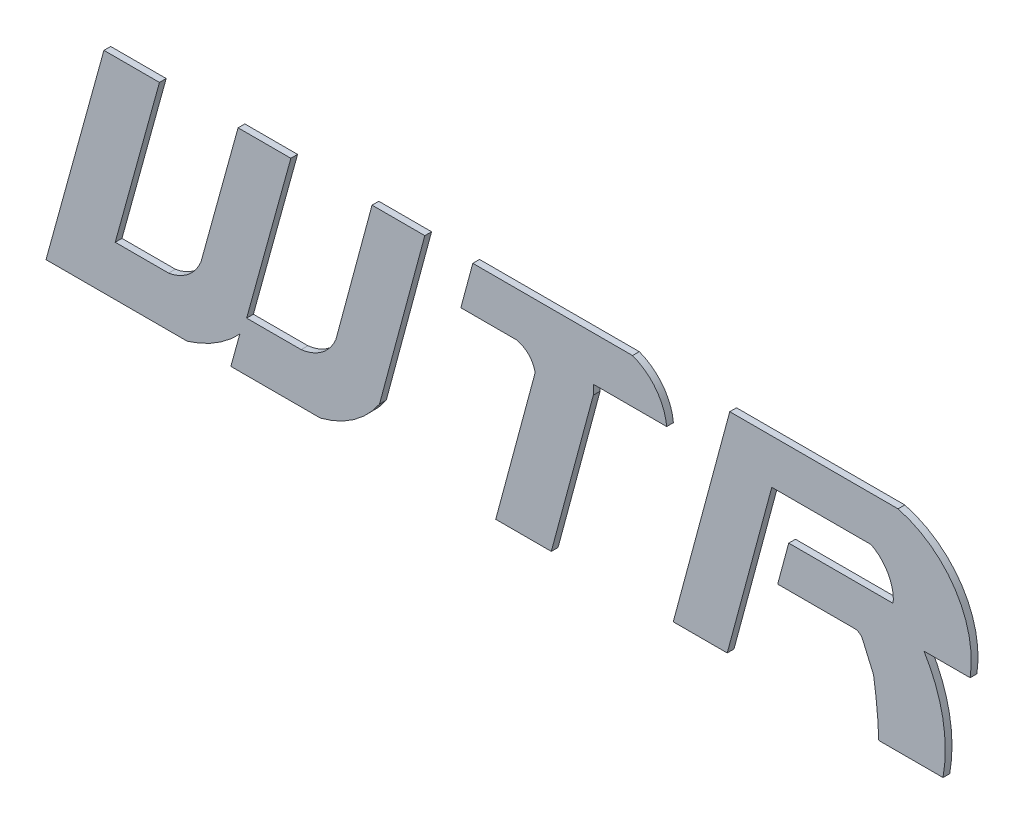
SolidWorks part; units mm, degrees
ref_plane "Front" through (0, 0, 0) normal (0, 0, 1) x (1, 0, 0)
ref_plane "Top" through (0, 0, 0) normal (0, 1, 0) x (1, 0, 0)
ref_plane "Right" through (0, 0, 0) normal (1, 0, 0) x (0, 0, -1)
sketch "草图2" plane through (0, 0, 0) normal (0, 0, 1) x (1, 0, 0)
  line L0 (341.3333, 1024) -> (1706.6667, 1024) construction
  line L1 (389.3044, 1163.2358) -> (303.4742, 851.6607)
  line L2 (303.4742, 851.6607) -> (512.7586, 851.6607)
  line L3 (577.4252, 851.6607) -> (710.2855, 851.6607)
  line L4 (389.3044, 1163.2358) -> (471.6072, 1163.2358)
  line L5 (471.6072, 1163.2358) -> (406.058, 925.2832)
  line L6 (406.058, 925.2832) -> (485.1876, 925.2832)
  line L7 (588.1245, 1163.2358) -> (533.2003, 963.8531)
  line L8 (588.1245, 1163.2358) -> (666.3345, 1163.2358)
  line L9 (666.3345, 1163.2358) -> (600.7853, 925.2832)
  line L10 (600.7853, 925.2832) -> (681.6483, 925.2832)
  line L11 (786.6575, 1163.2358) -> (733.0591, 963.8531)
  line L12 (786.6575, 1163.2358) -> (864.8674, 1163.2358)
  line L13 (864.8674, 1163.2358) -> (797.7177, 913.4432)
  line L14 (918.2572, 1097.3573) -> (935.9667, 1163.2358)
  line L15 (935.9667, 1163.2358) -> (1172.7019, 1163.2358)
  line L16 (918.2572, 1097.3573) -> (1000.5553, 1097.3573)
  line L17 (1114.5647, 1097.3573) -> (1223.2888, 1097.3573)
  line L18 (969.9365, 851.6607) -> (1028.3503, 1068.9564)
  line L19 (969.9365, 851.6607) -> (1052.2954, 851.6607)
  line L20 (1052.2954, 851.6607) -> (1114.5647, 1083.2984)
  line L21 (1114.5647, 1097.3573) -> (1114.5647, 1083.2984)
  line L22 (1316.7648, 1163.2358) -> (1233.0067, 851.6607)
  line L23 (1233.0067, 851.6607) -> (1313, 851.6607)
  line L24 (1313, 851.6607) -> (1379.0486, 1097.3573)
  line L25 (1379.0486, 1097.3573) -> (1526.2836, 1097.3573)
  line L26 (1316.7648, 1163.2358) -> (1566.1682, 1163.2358)
  line L27 (1604.5506, 999.8486) -> (1673, 999.8486)
  line L28 (1558.9709, 1038.2308) -> (1404.1293, 1038.2308)
  line L29 (1404.1293, 1038.2308) -> (1387.7741, 977.3907)
  line L30 (1387.7741, 977.3907) -> (1499.9591, 977.3907)
  line L31 (1513.7437, 969.2578) -> (1529.8482, 932.0508)
  line L32 (1537.5971, 851.6607) -> (1632.7974, 851.6607)
  line L33 (577.4252, 851.6607) -> (590.6328, 899.6064)
  arc A0 (485.1876, 925.2832) -> (533.2003, 963.8531) centre (475.2441, 986.8296) ccw
  arc A1 (681.6483, 925.2832) -> (733.0591, 963.8531) centre (674.2809, 988.6516) ccw
  arc A2 (1000.5553, 1097.3573) -> (1028.3503, 1068.9564) centre (993.9959, 1063.1364) cw
  arc A3 (1172.7019, 1163.2358) -> (1223.2888, 1097.3573) centre (1145.0074, 1089.608) cw
  arc A4 (1529.8482, 932.0508) -> (1537.5971, 851.6607) centre (882.7224, 829.1054) cw
  arc A5 (1632.7974, 851.6607) -> (1604.5506, 999.8486) centre (1425.4931, 888.9315) ccw
  arc A6 (1513.7437, 969.2578) -> (1499.9591, 977.3907) centre (1501.2656, 963.8568) ccw
  arc A7 (1566.1682, 1163.2358) -> (1673, 999.8486) centre (1528.7599, 1022.1562) cw
  arc A8 (710.2855, 851.6607) -> (797.7177, 913.4432) centre (672.9168, 997.3) ccw
  arc A9 (512.7586, 851.6607) -> (590.6328, 899.6064) centre (460.87, 1023.1543) ccw
  arc A10 (1558.9709, 1038.2308) -> (1526.2836, 1097.3573) centre (1497.8762, 1043.0541) ccw
extrude "凸台-拉伸1" add sketch "草图2" along normal blind 10
